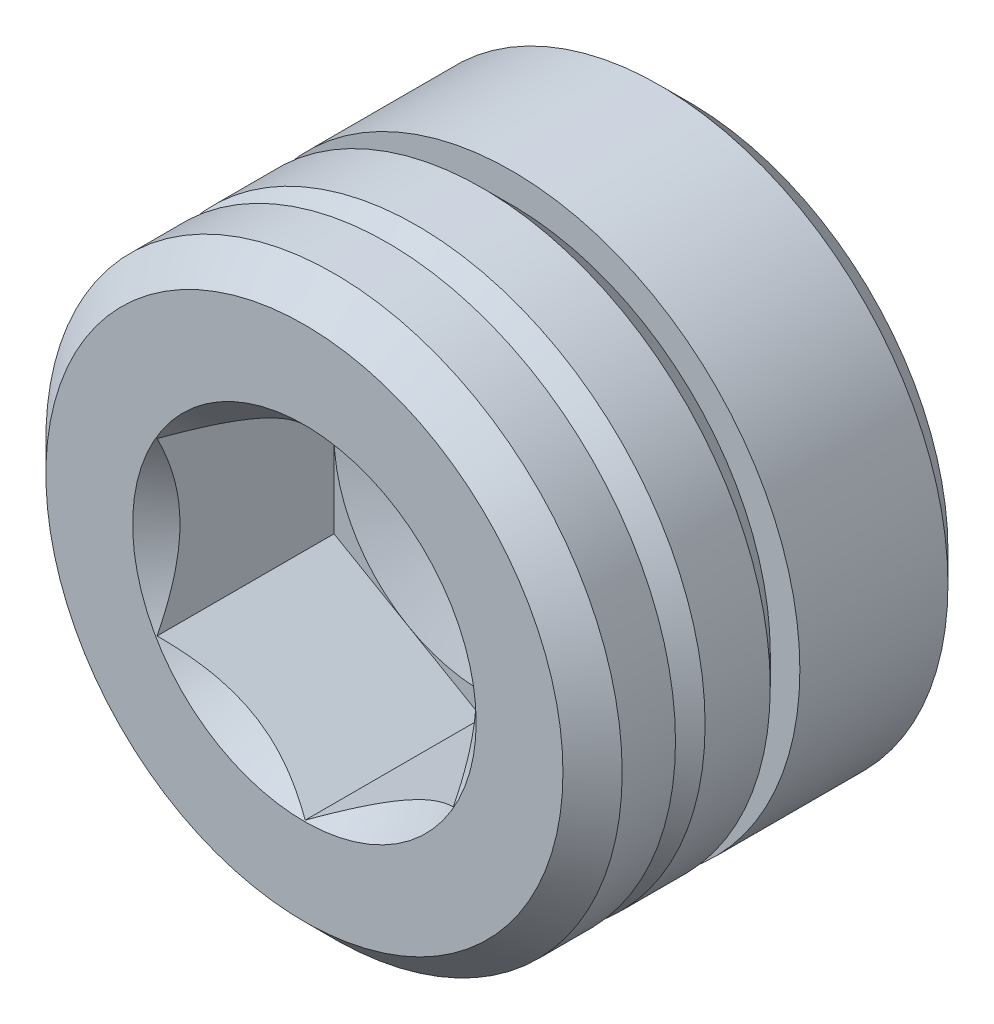
SolidWorks part; units mm, degrees
ref_plane "Front Plane" through (0, 0, 0) normal (0, 0, 1) x (1, 0, 0)
ref_plane "Top Plane" through (0, 0, 0) normal (0, 1, 0) x (1, 0, 0)
ref_plane "Right Plane" through (0, 0, 0) normal (1, 0, 0) x (0, 0, -1)
ref_plane "Plane1" through (0, 0, 0) normal (1, 0, 0) x (0, 0, -1)
sketch "Sketch1" plane through (0, 0, 0) normal (1, 0, 0) x (0, 0, -1)
  line L0 (0, 0) -> (0, 4.365)
  line L1 (0, 4.365) -> (0.5, 4.865)
  line L2 (0.5, 4.865) -> (6, 4.865)
  line L3 (6, 4.865) -> (6.5, 4.365)
  line L4 (6.5, 4.365) -> (6.5, 0)
  line L5 (6.5, 0) -> (0, 0)
  line L6 (6.5, 0) -> (0, 0) construction
revolve "Revolve1" add sketch "Sketch1" angle 360 about L6
cosmetic thread "Cosmetic Thread1" parameters "D1"=1.4, "D2"=8.566
cosmetic thread "Cosmetic Thread2" parameters "D1"=3, "D2"=8.566
ref_plane "Plane2" through (0, 0, 0) normal (1, 0, 0) x (0, 0, -1)
sketch "Sketch2" plane through (0, 0, 0) normal (1, 0, 0) x (0, 0, -1)
  line L0 (0, 4.865) -> (1.4, 4.865)
  line L1 (1.4, 4.865) -> (1.4, 4.365)
  line L2 (1.4, 4.365) -> (1.9, 4.865)
  line L3 (1.9, 4.865) -> (3, 4.865)
  line L4 (3, 4.865) -> (3.5, 4.365)
  line L5 (3.5, 4.365) -> (3.5, 4.865)
  line L6 (3.5, 4.865) -> (6.5, 4.865)
  line L7 (6.5, 4.865) -> (6.5, 9.865)
  line L8 (6.5, 9.865) -> (0, 9.865)
  line L9 (0, 9.865) -> (0, 4.865)
  line L10 (6.5, 0) -> (0, 0) construction
revolve "Cut-Revolve1" cut sketch "Sketch2" angle 360 about L10
ref_plane "Plane3" through (0, 0, 0) normal (1, 0, 0) x (0, 0, -1)
sketch "Sketch3" plane through (0, 0, 0) normal (1, 0, 0) x (0, 0, -1)
  line L0 (0, 0) -> (0, 2.9)
  line L1 (0, 2.9) -> (0.4, 2.5)
  line L2 (0.4, 2.5) -> (3, 2.5)
  line L3 (3, 2.5) -> (3.6933, 0)
  line L4 (3.6933, 0) -> (0, 0)
  line L5 (3.6933, 0) -> (0, 0) construction
revolve "Cut-Revolve2" cut sketch "Sketch3" angle 360 about L5
ref_plane "Plane4" through (0, 0, 0) normal (0, 0, 1) x (1, 0, 0)
sketch "Sketch4" plane through (0, 0, 0) normal (0, 0, 1) x (1, 0, 0)
  line L0 (-2.5, -1.4434) -> (0, -2.8868)
  line L1 (0, -2.8868) -> (2.5, -1.4434)
  line L2 (2.5, -1.4434) -> (2.5, 1.4434)
  line L3 (2.5, 1.4434) -> (0, 2.8868)
  line L4 (0, 2.8868) -> (-2.5, 1.4434)
  line L5 (-2.5, 1.4434) -> (-2.5, -1.4434)
extrude "Cut-Extrude1" cut sketch "Sketch4" against normal blind 3
